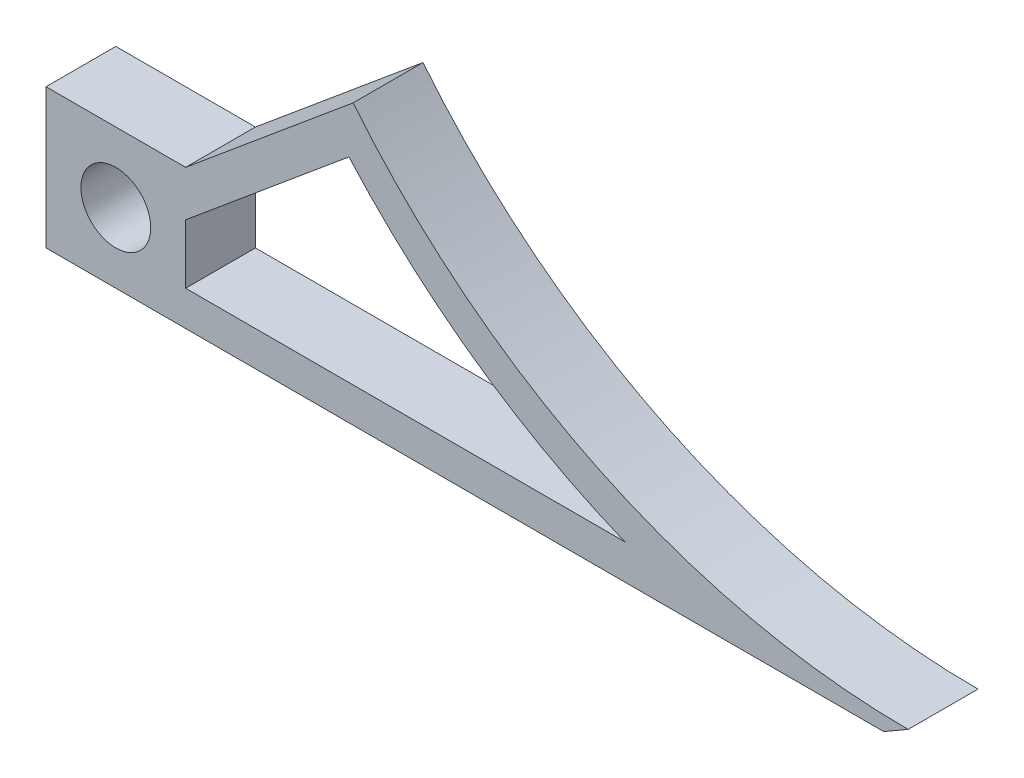
SolidWorks part; units mm, degrees
material "AISI Type A2 Tool Steel"
ref_plane "Front Plane" through (0, 0, 0) normal (0, 0, 1) x (1, 0, 0)
ref_plane "Top Plane" through (0, 0, 0) normal (0, 1, 0) x (1, 0, 0)
ref_plane "Right Plane" through (0, 0, 0) normal (1, 0, 0) x (0, 0, -1)
sketch "Sketch1" plane through (0, 0, 0) normal (0, 0, 1) x (1, 0, 0)
  line L0 (6.35, 6.35) -> (21.59, 19.05)
  line L1 (-6.35, -6.35) -> (6.35, -6.35)
  line L2 (-6.35, -6.35) -> (-6.35, 6.35)
  line L3 (-6.35, 6.35) -> (6.35, 6.35)
  line L4 (6.35, -6.35) -> (6.35, 6.35) construction
  line L5 (-6.35, -6.35) -> (6.35, 6.35) construction
  line L6 (-6.35, 6.35) -> (6.35, -6.35) construction
  line L7 (6.35, -6.35) -> (69.85, -6.35)
  line L8 (21.59, 19.05) -> (69.85, -6.35) construction
  line L9 (69.85, -6.35) -> (72.0752, -5.0653)
  line L10 (72.0752, -5.0653) -> (6.35, -5.0653) construction
  line L11 (8.3826, 3.9109) -> (21.2048, 14.5961) construction
  line L12 (46.3068, -3.175) -> (46.3068, -3.175)
  line L13 (6.35, -3.175) -> (46.3068, -3.175)
  line L14 (21.2048, 14.5961) -> (6.35, 2.2171)
  line L15 (6.35, 2.2171) -> (6.35, -3.175)
  circle A0 centre (0, 0) radius 3.175
  arc A1 (21.59, 19.05) -> (72.0752, -5.0653) centre (72.0752, 59.8377) ccw
  arc A2 (21.2048, 14.5961) -> (46.3068, -3.175) centre (72.0752, 59.8377) ccw
  point P0 (0, 0)
  dimension "D4" = 6.35
  dimension "D1" = 12.7
  dimension "D3" = 63.5
  dimension "D5" = 2.5695
  dimension "D6" = 30
  dimension "D7" = 25.4
  dimension "D8" = 15.24
  dimension "D9" = 3.175
extrude "Boss-Extrude1" add sketch "Sketch1" along normal blind 6.35
